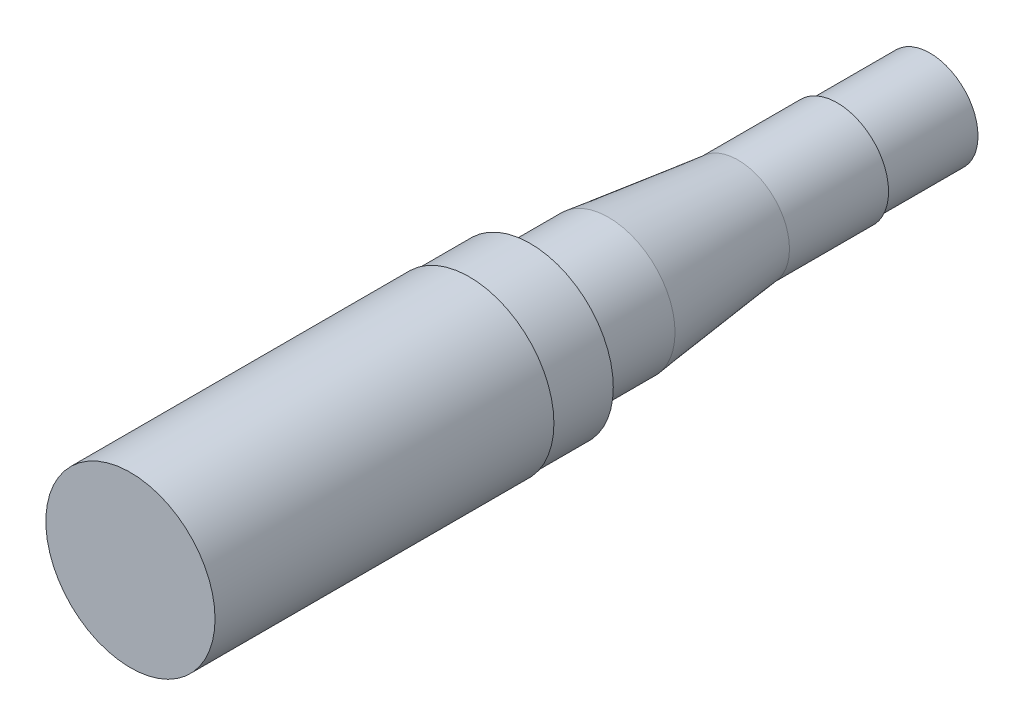
SolidWorks part; units mm, degrees
material "ASTM A36 Steel"
ref_plane "Front Plane" through (0, 0, 0) normal (0, 0, 1) x (1, 0, 0)
ref_plane "Top Plane" through (0, 0, 0) normal (0, 1, 0) x (1, 0, 0)
ref_plane "Right Plane" through (0, 0, 0) normal (1, 0, 0) x (0, 0, -1)
sketch "Sketch1" plane through (0, 0, 0) normal (1, 0, 0) x (0, 0, -1)
  line L0 (0, 0) -> (0, 22.225)
  line L1 (0, 55) -> (0, -55) construction
  line L2 (0, 22.225) -> (89.027, 22.225)
  line L3 (89.027, 22.225) -> (89.027, 21.8186)
  line L4 (89.027, 21.8186) -> (105.029, 21.8186)
  line L5 (105.029, 21.8186) -> (105.029, 19.3675)
  line L6 (106.934, 17.4625) -> (125.603, 17.4625)
  line L7 (125.603, 17.4625) -> (159.639, 13.4874)
  line L8 (159.639, 13.4874) -> (185.674, 13.4874)
  line L9 (185.674, 13.4874) -> (185.674, 13.2334)
  line L10 (186.309, 12.5984) -> (188.214, 12.5984)
  line L11 (188.214, 12.5984) -> (210.058, 12.5984)
  line L12 (210.058, 12.5984) -> (210.058, 0)
  line L13 (0, 0) -> (210.058, 0) construction
  line L14 (0, 0) -> (210.058, 0)
  arc A0 (105.029, 19.3675) -> (106.934, 17.4625) centre (106.934, 19.3675) ccw
  arc A1 (185.674, 13.2334) -> (186.309, 12.5984) centre (186.309, 13.2334) ccw
  dimension "D2" = 1.905
  dimension "D3" = 0.635
  dimension "D1" = 44.45
  dimension "D4" = 89.027
  dimension "D5" = 16.002
  dimension "D6" = 20.574
  dimension "D7" = 105.029
  dimension "D8" = 54.61
  dimension "D9" = 80.645
  dimension "D10" = 2.54
  dimension "D11" = 43.6372
  dimension "D12" = 34.925
  dimension "D13" = 26.9748
  dimension "D14" = 25.1968
revolve "Revolve1" add sketch "Sketch1" angle 360 mid plane about L13
